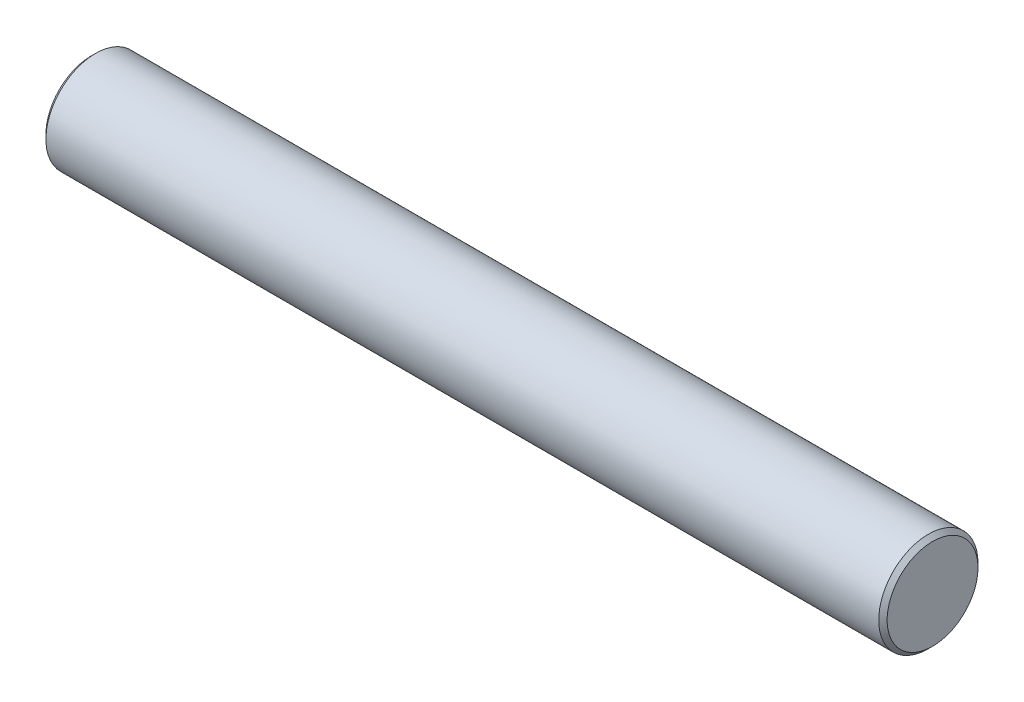
SolidWorks part; units mm, degrees
material "Alloy Steel (SS)"
ref_plane "Front Plane" through (0, 0, 0) normal (0, 0, 1) x (1, 0, 0)
ref_plane "Top Plane" through (0, 0, 0) normal (0, 1, 0) x (1, 0, 0)
ref_plane "Right Plane" through (0, 0, 0) normal (1, 0, 0) x (0, 0, -1)
sketch "Sketch1" plane through (0, 0, 0) normal (0, 0, 1) x (1, 0, 0)
  line L0 (-12.7, 0) -> (12.7, 0) construction
  line L1 (0, 0) -> (0, 23.8199) construction
  line L2 (-12.573, 1.4986) -> (12.573, 1.4986)
  line L3 (12.7, 1.3716) -> (12.7, 0)
  line L4 (12.573, 1.4986) -> (12.7, 1.3716)
  line L5 (-12.573, 1.4986) -> (-12.7, 1.3716)
  line L6 (-12.7, 1.3716) -> (-12.7, 0)
  line L7 (12.7, 0) -> (-12.7, 0)
  point P3 (-12.7, 1.4986)
  point P5 (12.7, 1.4986)
  point P11 (0, 1.4986)
  dimension "D1" = 12.7
  dimension "D2" = 2.9972
revolve "Revolve1" add sketch "Sketch1" angle 360 about L7
